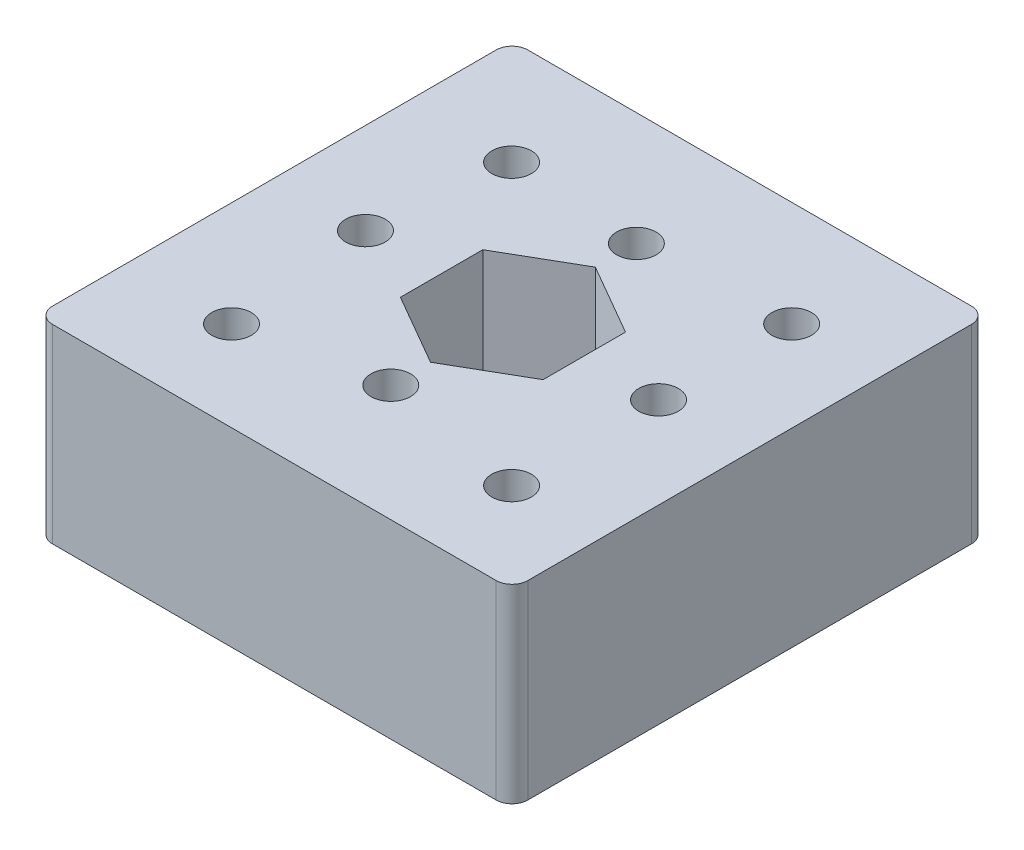
SolidWorks part; units mm, degrees
ref_plane "Front Plane" through (0, 0, 0) normal (0, 0, 1) x (1, 0, 0)
ref_plane "Top Plane" through (0, 0, 0) normal (0, 1, 0) x (1, 0, 0)
ref_plane "Right Plane" through (0, 0, 0) normal (1, 0, 0) x (0, 0, -1)
sketch "Sketch1" plane through (0, 0, 0) normal (0, 1, 0) x (1, 0, 0)
  line L7 (4.5033, -2.5408) -> (4.5033, 2.6592)
  line L8 (4.5033, 2.6592) -> (0, 5.2592)
  line L9 (0, 5.2592) -> (-4.5033, 2.6592)
  line L10 (-4.5033, 2.6592) -> (-4.5033, -2.5408)
  line L11 (-4.5033, -2.5408) -> (0, -5.1408)
  line L12 (0, -5.1408) -> (4.5033, -2.5408)
  line L13 (-15, 15) -> (15, 15)
  line L14 (-15, 15) -> (-15, -15)
  line L15 (-15, -15) -> (15, -15)
  line L16 (15, 15) -> (15, -15)
  line L17 (-15, 15) -> (15, -15) construction
  line L18 (-15, -15) -> (15, 15) construction
  circle A0 centre (-9.25, 0) radius 1.25
  circle A1 centre (9.25, 0) radius 1.25
  circle A2 centre (0, 7.8486) radius 1.25
  circle A3 centre (0, -7.6514) radius 1.25
  circle A4 centre (9.3009, 8.3513) radius 1.25
  circle A5 centre (9.3009, -9.3264) radius 1.25
  circle A6 centre (-8.3768, -9.3264) radius 1.25
  circle A7 centre (-8.3768, 8.3513) radius 1.25
  point P9 (0, 0)
  point P27 (0.462, -0.4876)
  dimension "D4" = 2.5
  dimension "D6" = 2.5
  dimension "D9" = 30
  dimension "D1" = 5.2
  dimension "D2" = 18.5
  dimension "D3" = 9.25
  dimension "D5" = 15.5
  dimension "D7" = 12.5
  dimension "D8" = 4
extrude "Boss-Extrude2" add sketch "Sketch1" along normal blind 12
fillet "Fillet1" radius 1 4 edges at (-15, 6, -15) (-15, 6, 15) (15, 6, -15) (15, 6, 15)
